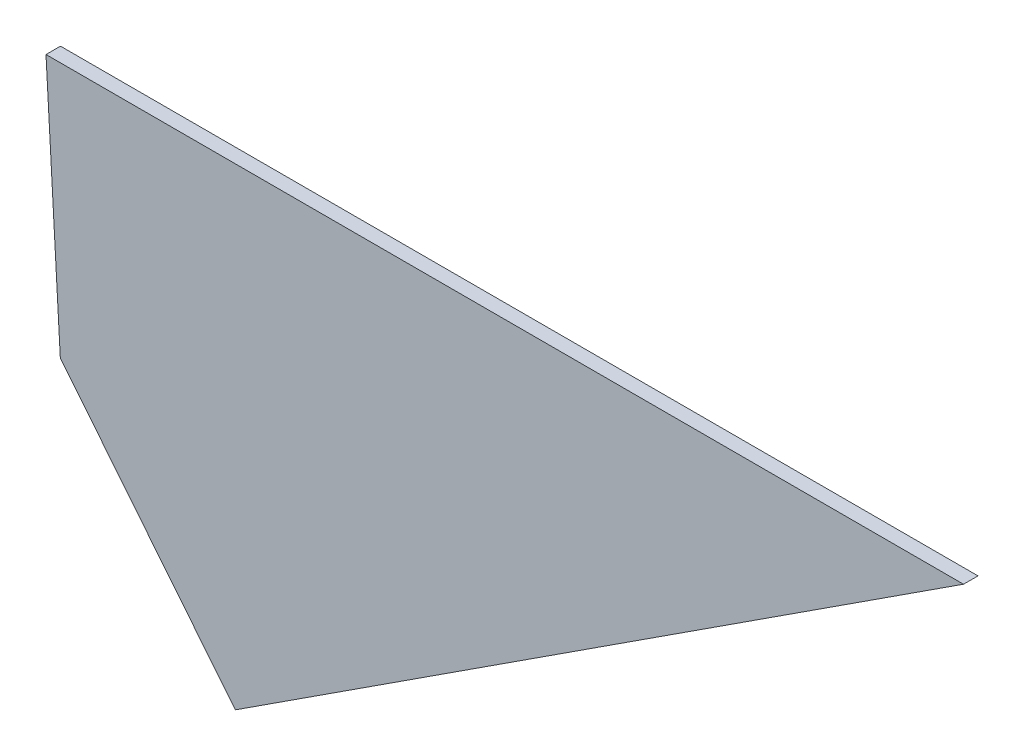
SolidWorks part; units mm, degrees
ref_plane "Plan de face" through (0, 0, 0) normal (0, 0, 1) x (1, 0, 0)
ref_plane "Plan de dessus" through (0, 0, 0) normal (0, 1, 0) x (1, 0, 0)
ref_plane "Plan de droite" through (0, 0, 0) normal (1, 0, 0) x (0, 0, -1)
sketch "Esquisse1" plane through (0, 0, 0) normal (0, 0, 1) x (1, 0, 0)
  line L0 (58.6876, -38.6363) -> (-92.2731, -136.6714)
  line L1 (-92.2731, -136.6714) -> (-125.3272, -95.6363)
  line L2 (-125.3272, -95.6363) -> (-128.5181, -38.6363) construction
  line L3 (-128.5181, -38.6363) -> (58.6876, -38.6363)
  line L13 (-128.5181, -38.6363) -> (-131.5228, -38.6363)
  line L14 (-131.5228, -38.6363) -> (-128.5563, -91.6276)
  line L15 (-128.5563, -91.6276) -> (-125.3272, -95.6363)
  dimension "D1" = 33
  dimension "D2" = 180
  dimension "D3" = 57
  dimension "D4" = 3
extrude "Boss.-Extru.1" add sketch "Esquisse1" against normal blind 3
